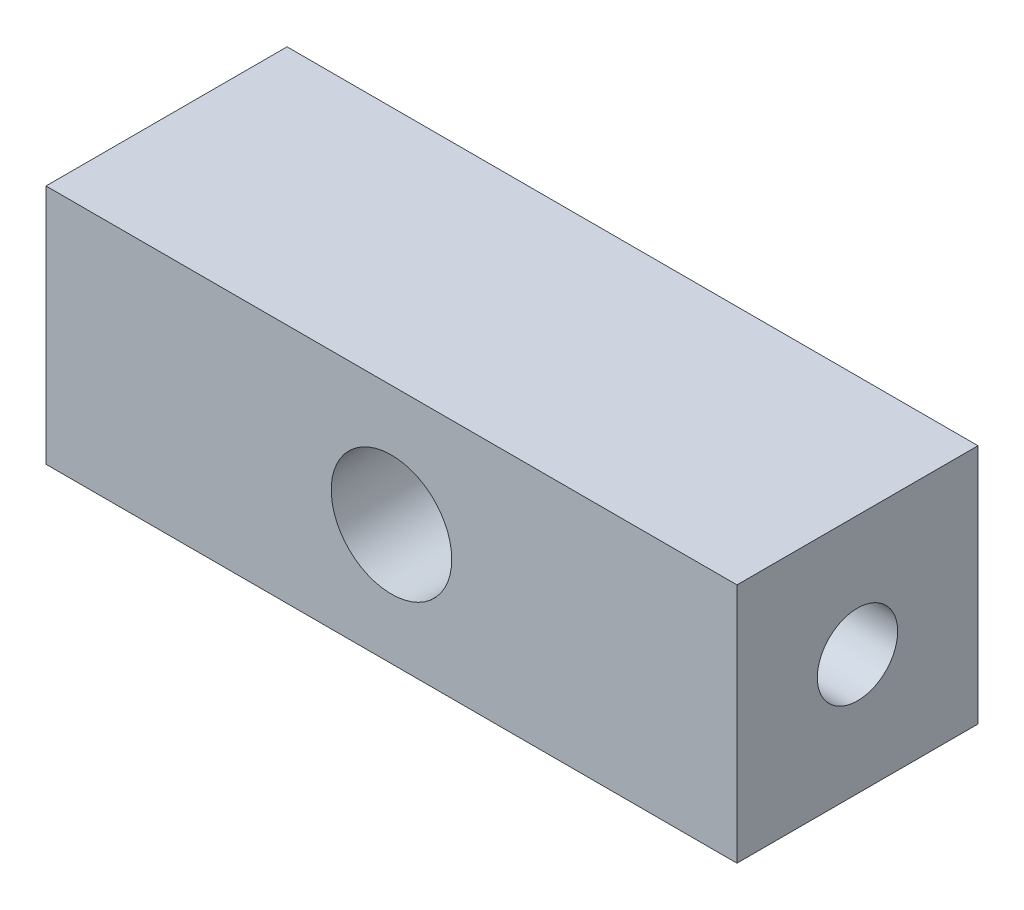
SolidWorks part; units mm, degrees
ref_plane "Alzado" through (0, 0, 0) normal (0, 0, 1) x (1, 0, 0)
ref_plane "Planta" through (0, 0, 0) normal (0, 1, 0) x (1, 0, 0)
ref_plane "Vista lateral" through (0, 0, 0) normal (1, 0, 0) x (0, 0, -1)
sketch "Croquis1" plane through (0, 0, 0) normal (0, 0, 1) x (1, 0, 0)
  line L1 (-43, -15) -> (43, -15)
  line L2 (-43, -15) -> (-43, 15)
  line L3 (-43, 15) -> (43, 15)
  line L4 (43, -15) -> (43, 15)
  line L5 (-43, -15) -> (43, 15) construction
  line L6 (-43, 15) -> (43, -15) construction
  circle A0 centre (0, 0) radius 7.5
  point P0 (0, 0)
  dimension "D3" = 15
  dimension "D1" = 30
  dimension "D2" = 86
extrude "Saliente-Extruir1" add sketch "Croquis1" along normal mid plane 30
sketch "Croquis2" plane through (43, 0, 0) normal (1, 0, 0) x (0, 0, -1)
  circle A0 centre (0, 0) radius 5
  dimension "D1" = 10
extrude "Cortar-Extruir1" cut sketch "Croquis2" against normal through all
